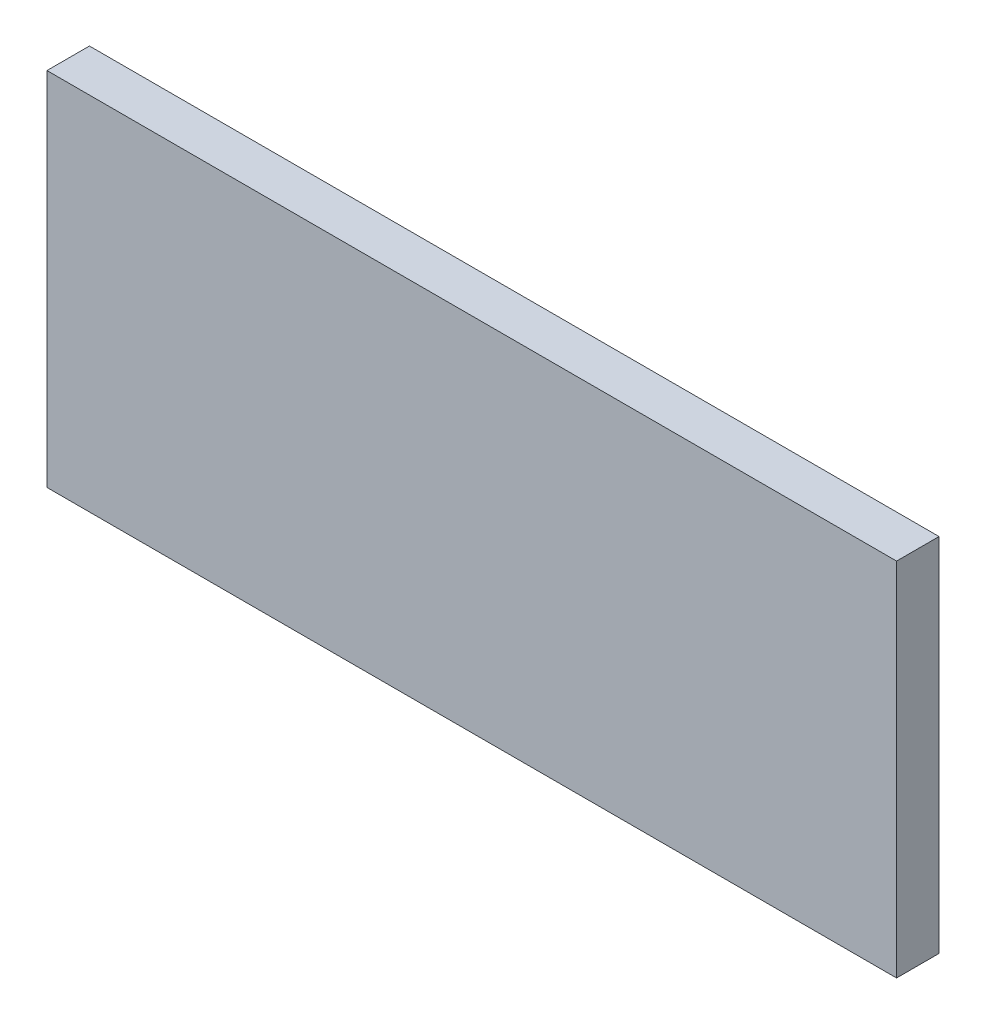
SolidWorks part; units mm, degrees
ref_plane "Front Plane" through (0, 0, 0) normal (0, 0, 1) x (1, 0, 0)
ref_plane "Top Plane" through (0, 0, 0) normal (0, 1, 0) x (1, 0, 0)
ref_plane "Right Plane" through (0, 0, 0) normal (1, 0, 0) x (0, 0, -1)
sketch "Sketch1" plane through (0, 0, 0) normal (0, 0, 1) x (1, 0, 0)
  line L1 (0, 0) -> (-2000, 0)
  line L2 (0, 0) -> (0, -850)
  line L3 (0, -850) -> (-2000, -850)
  line L4 (-2000, 0) -> (-2000, -850)
  dimension "D1" = 850
  dimension "D2" = 2000
extrude "Boss-Extrude1" add sketch "Sketch1" along normal blind 100
